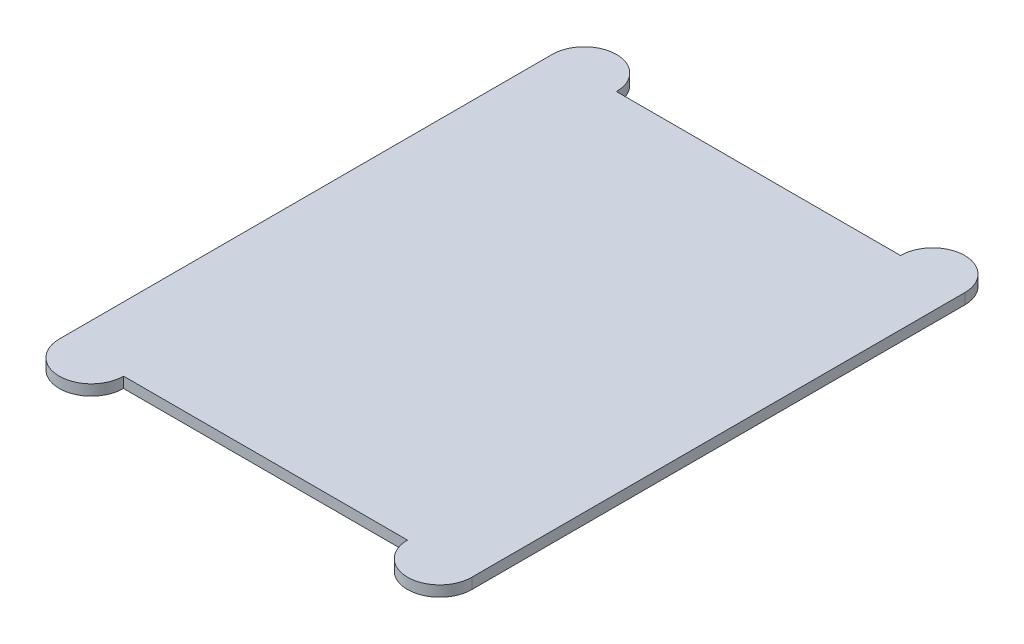
SolidWorks part; units mm, degrees
material "1100-H12 Rod (SS)"
ref_plane "Front Plane" through (0, 0, 0) normal (0, 0, 1) x (1, 0, 0)
ref_plane "Top Plane" through (0, 0, 0) normal (0, 1, 0) x (1, 0, 0)
ref_plane "Right Plane" through (0, 0, 0) normal (1, 0, 0) x (0, 0, -1)
sketch "Sketch1" plane through (0, 0, 0) normal (0, 1, 0) x (1, 0, 0)
  line L0 (0, 0) -> (0, -398.4774) construction
  line L1 (-132.5, 230) -> (132.5, 230)
  line L2 (-192.5, 230) -> (-192.5, -230)
  line L3 (-132.5, -230) -> (132.5, -230)
  line L4 (192.5, 230) -> (192.5, -230)
  line L5 (-192.5, 230) -> (192.5, -230) construction
  line L6 (-192.5, -230) -> (192.5, 230) construction
  line L7 (0, 0) -> (424.0329, 0) construction
  arc A0 (-192.5, 230) -> (-132.5, 230) centre (-162.5, 230) cw
  arc A1 (-192.5, -230) -> (-132.5, -230) centre (-162.5, -230) ccw
  arc A2 (192.5, -230) -> (132.5, -230) centre (162.5, -230) cw
  arc A3 (192.5, 230) -> (132.5, 230) centre (162.5, 230) ccw
  point P0 (0, 0)
  point P10 (-162.5, 260)
  dimension "D1" = 460
  dimension "D2" = 385
  dimension "D3" = 30
extrude "Boss-Extrude1" add sketch "Sketch1" along normal blind 10
sketch "Sketch2" plane through (0, 0, 0) normal (0, -1, 0) x (1, 0, 0)
  line L1 (-100, 150) -> (100, 150)
  line L2 (-100, 150) -> (-100, -150)
  line L3 (-100, -150) -> (100, -150)
  line L4 (100, 150) -> (100, -150)
  line L5 (-100, 150) -> (100, -150) construction
  line L6 (-100, -150) -> (100, 150) construction
  point P0 (0, 0)
  dimension "D1" = 200
  dimension "D2" = 300
extrude "Boss-Extrude2" add sketch "Sketch2" along normal blind 5
sketch "Sketch3" plane through (0, -5, 0) normal (0, -1, 0) x (1, 0, 0)
  line L0 (0, 0) -> (0, 189.0824) construction
  line L1 (-100, 150) -> (100, 150)
  line L2 (-100, 150) -> (-100, -150)
  line L3 (-100, -150) -> (100, -150)
  line L4 (100, 150) -> (100, -150)
  line L5 (-100, 150) -> (100, -150) construction
  line L6 (-100, -150) -> (100, 150) construction
  line L7 (0, 189.0824) -> (0, 0) construction
  line L8 (0, 0) -> (-167.4871, 0) construction
  circle A0 centre (72.1142, 0) radius 10
  circle A1 centre (-73.2786, 0) radius 10
  circle A2 centre (-73.2786, 75) radius 10
  circle A3 centre (72.1142, 75) radius 10
  circle A4 centre (72.1142, -75) radius 10
  circle A5 centre (-73.2786, -75) radius 10
  point P0 (0, 0)
  dimension "D1" = 20
  dimension "D2" = 20
  dimension "D3" = 20
  dimension "D4" = 20
  dimension "D5" = 20
  dimension "D6" = 20
  dimension "D7" = 75
  dimension "D8" = 75
  dimension "D9" = 75
  dimension "D10" = 75
extrude "Boss-Extrude3" add sketch "Sketch3" along normal blind 10
sketch "Sketch4" plane through (0, -5, 0) normal (0, -1, 0) x (1, 0, 0)
  circle A0 centre (-73.2786, 75) radius 2.5
  circle A1 centre (72.1142, 75) radius 2.5
  circle A2 centre (-73.2786, 0) radius 2.5
  circle A3 centre (-73.2786, -75) radius 2.5
  circle A4 centre (72.1142, 0) radius 2.5
  circle A5 centre (72.1142, -75) radius 2.5
  dimension "D1" = 5
  dimension "D2" = 5
  dimension "D3" = 5
  dimension "D4" = 5
  dimension "D5" = 5
  dimension "D6" = 5
extrude "Boss-Extrude4" add sketch "Sketch4" along normal blind 25
sketch "Sketch5" plane through (0, -30, 0) normal (0, -1, 0) x (1, 0, 0)
  circle A0 centre (-73.2786, 0) radius 10
  circle A1 centre (-73.2786, 75) radius 10
  circle A2 centre (72.1142, 75) radius 10
  circle A3 centre (72.1142, 0) radius 10
  circle A4 centre (72.1142, -75) radius 10
  circle A5 centre (-73.2786, -75) radius 10
extrude "Boss-Extrude5" add sketch "Sketch5" along normal blind 2
sketch "Sketch6" plane through (0, -15, 0) normal (0, -1, 0) x (1, 0, 0)
  line L0 (0, 130.1235) -> (0, 150) construction
  line L1 (-52.5, 130.1235) -> (52.5, 130.1235)
  line L2 (-52.5, 130.1235) -> (-52.5, 115.1235)
  line L3 (-52.5, 115.1235) -> (52.5, 115.1235)
  line L4 (52.5, 130.1235) -> (52.5, 115.1235)
  line L5 (-52.5, 130.1235) -> (52.5, 115.1235) construction
  line L6 (-52.5, 115.1235) -> (52.5, 130.1235) construction
  line L7 (100, 150) -> (-100, 150) construction
  line L8 (0, 0) -> (209.4771, 0) construction
  line L9 (-52.5, -130.1235) -> (-52.5, -115.1235)
  line L10 (-52.5, -115.1235) -> (52.5, -115.1235)
  line L11 (52.5, -130.1235) -> (52.5, -115.1235)
  line L12 (-52.5, -130.1235) -> (52.5, -130.1235)
  point P0 (0, 122.6235)
  dimension "D1" = 105
  dimension "D2" = 15
extrude "Boss-Extrude6" add sketch "Sketch6" along normal blind 50
sketch "Sketch7" plane through (0, 0, 130.1235) normal (0, 0, 1) x (1, 0, 0)
  line L0 (52.5, -65) -> (-52.5, -65) construction
  line L3 (-52.5, -65) -> (-52.5, -15) construction
  line L4 (52.5, -65) -> (52.5, -15) construction
  circle A0 centre (37.5, -40) radius 10
  circle A1 centre (-37.5, -40) radius 10
  dimension "D1" = 20
  dimension "D2" = 25
  dimension "D3" = 15
  dimension "D4" = 15
extrude "Cut-Extrude1" cut sketch "Sketch7" against normal through all
sketch "Sketch8" plane through (0, 0, 0) normal (0, -1, 0) x (1, 0, 0)
  line L0 (-192.5, -230) -> (-192.5, 230) construction
  line L1 (192.5, 230) -> (192.5, -230) construction
  line L2 (-132.5, 230) -> (132.5, 230) construction
  circle A0 centre (157.5, 0) radius 25
  circle A1 centre (-157.5, 0) radius 25
  dimension "D1" = 50
  dimension "D2" = 35
  dimension "D3" = 35
  dimension "D4" = 230
extrude "Boss-Extrude7" add sketch "Sketch8" along normal blind 5
sketch "Sketch9" plane through (0, 0, 130.1235) normal (0, 0, 1) x (1, 0, 0)
  circle A0 centre (37.5, -40) radius 10
  circle A1 centre (-37.5, -40) radius 10
extrude "Boss-Extrude8" add sketch "Sketch9" along normal blind 20 and the other way up to surface (15 mm away) separate body other way up to face at (47.5, -40, 115.1235)
sketch "Sketch10" plane through (0, 0, -130.1235) normal (0, 0, -1) x (-1, 0, 0)
  circle A0 centre (37.5, -40) radius 10
  circle A1 centre (-37.5, -40) radius 10
extrude "Boss-Extrude10" add sketch "Sketch10" along normal blind 20 and the other way blind 15
sketch "Sketch11" plane through (0, -15, 0) normal (0, -1, 0) x (1, 0, 0)
  circle A0 centre (0, 0) radius 12.5
  dimension "D1" = 25
extrude "Cut-Extrude2" cut sketch "Sketch11" against normal blind 1
